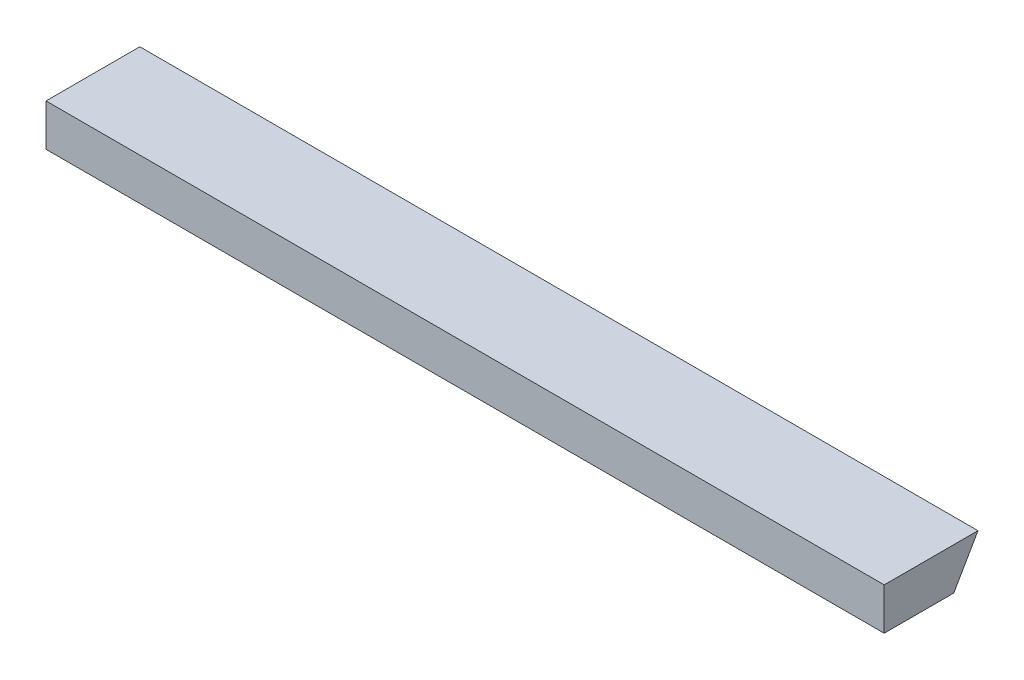
SolidWorks part; units mm, degrees
ref_plane "Front Plane" through (0, 0, 0) normal (0, 0, 1) x (1, 0, 0)
ref_plane "Top Plane" through (0, 0, 0) normal (0, 1, 0) x (1, 0, 0)
ref_plane "Right Plane" through (0, 0, 0) normal (1, 0, 0) x (0, 0, -1)
sketch "Sketch1" plane through (0, 0, 0) normal (1, 0, 0) x (0, 0, -1)
  line L14 (0, 0) -> (60.2242, 0)
  line L17 (60.2242, 0) -> (60.2242, -12)
  line L18 (0, 0) -> (0, -12)
  line L21 (0, -12) -> (60.2242, -12)
extrude "Boss-Extrude1" add sketch "Sketch1" against normal blind 240
extrude "Cut-Extrude1" cut sketch "Sketch2" against normal through all and the other way through all flip side to cut
sketch "Sketch2" plane through (0, -88.9963, -210.1405) normal (1, 0, 0) x (0, 0, -1)
  line L1 (-215.4122, 33.3453) -> (-115.1259, 207.0463)
